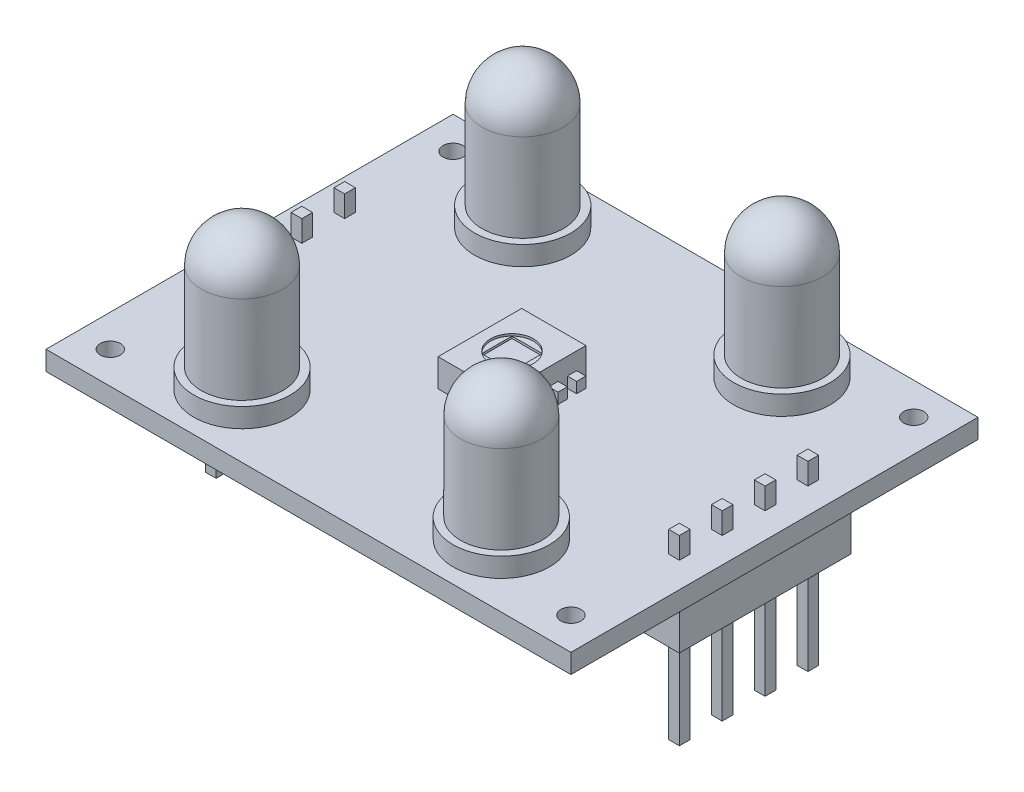
SolidWorks part; units mm, degrees
ref_plane "Plan de face" through (0, 0, 0) normal (0, 0, 1) x (1, 0, 0)
ref_plane "Plan de dessus" through (0, 0, 0) normal (0, 1, 0) x (1, 0, 0)
ref_plane "Plan de droite" through (0, 0, 0) normal (1, 0, 0) x (0, 0, -1)
sketch "Esquisse1" plane through (0, 0, 0) normal (0, 1, 0) x (1, 0, 0)
  line L1 (-15.5575, -12.065) -> (15.5575, -12.065)
  line L2 (-15.5575, -12.065) -> (-15.5575, 12.065)
  line L3 (-15.5575, 12.065) -> (15.5575, 12.065)
  line L4 (15.5575, -12.065) -> (15.5575, 12.065)
  line L5 (-15.5575, -12.065) -> (15.5575, 12.065) construction
  line L6 (-15.5575, 12.065) -> (15.5575, -12.065) construction
  line L7 (13.6525, -10.16) -> (-13.6525, -10.16) construction
  line L8 (13.6525, -10.16) -> (13.6525, 10.16) construction
  line L9 (13.6525, 10.16) -> (-13.6525, 10.16) construction
  line L10 (-13.6525, -10.16) -> (-13.6525, 10.16) construction
  line L11 (13.6525, -10.16) -> (-13.6525, 10.16) construction
  line L12 (13.6525, 10.16) -> (-13.6525, -10.16) construction
  circle A0 centre (-13.6525, 10.16) radius 0.5953
  circle A1 centre (13.6525, 10.16) radius 0.5953
  circle A2 centre (-13.6525, -10.16) radius 0.5953
  circle A3 centre (13.6525, -10.16) radius 0.5953
  point P0 (0, 0)
  point P6 (0, 0)
  dimension "D5" = 1.1906
  dimension "D1" = 31.115
  dimension "D2" = 24.13
  dimension "D3" = 1.905
  dimension "D4" = 1.905
extrude "Boss.-Extru.1" add sketch "Esquisse1" along normal mid plane 1.143
sketch "Esquisse2" plane through (0, 0, 0) normal (0, 0, 1) x (1, 0, 0)
  line L0 (-15.5575, 0.5715) -> (15.5575, 0.5715) construction
  line L1 (-1.905, 2.2225) -> (1.905, 2.2225)
  line L2 (-1.905, 2.2225) -> (-1.905, 0.5715)
  line L3 (-1.905, 0.5715) -> (1.905, 0.5715)
  line L4 (1.905, 2.2225) -> (1.905, 0.5715)
  line L5 (-1.905, 2.2225) -> (1.905, 0.5715) construction
  line L6 (-1.905, 0.5715) -> (1.905, 2.2225) construction
  point P0 (0, 1.397)
  dimension "D1" = 1.651
  dimension "D2" = 3.81
extrude "Boss.-Extru.2" add sketch "Esquisse2" along normal mid plane 4.953
sketch "Esquisse3" plane through (0, 0.5715, 0) normal (0, 1, 0) x (1, 0, 0)
  line L0 (1.905, -2.4765) -> (1.905, 2.4765) construction
  line L1 (1.905, 1.9262) -> (2.4553, 1.9262)
  line L2 (1.905, 1.9262) -> (1.905, 1.3758)
  line L3 (1.905, 1.3758) -> (2.4553, 1.3758)
  line L4 (2.4553, 1.9262) -> (2.4553, 1.3758)
  line L5 (2.1802, 1.3758) -> (2.1802, 0.8255) construction
  line L6 (1.905, 0.8255) -> (2.4553, 0.8255)
  line L7 (1.905, 0.8255) -> (1.905, 0.2752)
  line L8 (1.905, 0.2752) -> (2.4553, 0.2752)
  line L9 (2.4553, 0.8255) -> (2.4553, 0.2752)
  line L10 (1.905, -0.2752) -> (2.4553, -0.2752)
  line L11 (1.905, -0.2752) -> (1.905, -0.8255)
  line L12 (1.905, -0.8255) -> (2.4553, -0.8255)
  line L13 (2.4553, -0.2752) -> (2.4553, -0.8255)
  line L14 (1.905, -1.3758) -> (2.4553, -1.3758)
  line L15 (1.905, -1.3758) -> (1.905, -1.9262)
  line L16 (1.905, -1.9262) -> (2.4553, -1.9262)
  line L17 (2.4553, -1.3758) -> (2.4553, -1.9262)
  line L18 (2.1802, 0.2752) -> (2.1802, -0.2752) construction
  line L19 (2.1802, -0.8255) -> (2.1802, -1.3758) construction
  line L20 (2.1802, 1.9262) -> (2.1802, 2.4765) construction
  line L21 (2.1802, -1.9262) -> (2.1802, -2.4765) construction
  line L22 (-1.905, -2.4765) -> (1.905, -2.4765) construction
  line L23 (1.905, 2.4765) -> (-1.905, 2.4765) construction
extrude "Boss.-Extru.3" add sketch "Esquisse3" along normal blind 0.635
sketch "Esquisse9" plane through (0, -0.5715, 0) normal (0, -1, 0) x (1, 0, 0)
  line L0 (0, -5.2776) -> (0, 5.2776) construction
  line L1 (15, 5.08) -> (12.46, 5.08)
  line L2 (15, 5.08) -> (15, -5.08)
  line L3 (15, -5.08) -> (12.46, -5.08)
  line L4 (12.46, 5.08) -> (12.46, -5.08)
  line L5 (0, -1.5367) -> (0, 1.5367) construction
  point P6 (12.46, 0)
  dimension "D1" = 2.54
  dimension "D2" = 10.16
  dimension "D3" = 30
extrude "Boss.-Extru.6" add sketch "Esquisse9" along normal blind 2.667
sketch "Esquisse10" plane through (0, -3.2385, 0) normal (0, -1, 0) x (1, 0, 0)
  line L0 (12.46, 0) -> (15, 5.08) construction
  line L1 (12.46, 5.08) -> (12.46, -5.08) construction
  line L2 (13.73, 2.54) -> (13.73, 5.08) construction
  line L3 (15, 5.08) -> (12.46, 5.08) construction
  line L4 (12.46, 0) -> (15, -5.08) construction
  line L5 (13.73, -2.54) -> (13.73, -5.08) construction
  line L6 (12.46, -5.08) -> (15, -5.08) construction
  line L7 (13.73, 2.54) -> (13.73, 0) construction
  line L8 (13.4125, 4.1275) -> (14.0475, 4.1275)
  line L9 (13.4125, 4.1275) -> (13.4125, 3.4925)
  line L10 (13.4125, 3.4925) -> (14.0475, 3.4925)
  line L11 (14.0475, 4.1275) -> (14.0475, 3.4925)
  line L12 (13.4125, 4.1275) -> (14.0475, 3.4925) construction
  line L13 (13.4125, 3.4925) -> (14.0475, 4.1275) construction
  line L14 (3.0035, 0) -> (-3.0035, 0) construction
  line L15 (13.73, 0) -> (13.73, -2.54) construction
  line L17 (13.4125, 1.5875) -> (14.0475, 1.5875)
  line L18 (13.4125, 1.5875) -> (13.4125, 0.9525)
  line L19 (13.4125, 0.9525) -> (14.0475, 0.9525)
  line L20 (14.0475, 1.5875) -> (14.0475, 0.9525)
  line L21 (13.4125, 1.5875) -> (14.0475, 0.9525) construction
  line L22 (13.4125, 0.9525) -> (14.0475, 1.5875) construction
  line L23 (13.4125, -0.9525) -> (14.0475, -0.9525)
  line L24 (13.4125, -0.9525) -> (13.4125, -1.5875)
  line L25 (13.4125, -1.5875) -> (14.0475, -1.5875)
  line L26 (14.0475, -0.9525) -> (14.0475, -1.5875)
  line L27 (13.4125, -0.9525) -> (14.0475, -1.5875) construction
  line L28 (13.4125, -1.5875) -> (14.0475, -0.9525) construction
  line L29 (13.4125, -3.4925) -> (14.0475, -3.4925)
  line L30 (13.4125, -3.4925) -> (13.4125, -4.1275)
  line L31 (13.4125, -4.1275) -> (14.0475, -4.1275)
  line L32 (14.0475, -3.4925) -> (14.0475, -4.1275)
  line L33 (13.4125, -3.4925) -> (14.0475, -4.1275) construction
  line L34 (13.4125, -4.1275) -> (14.0475, -3.4925) construction
  point P13 (13.73, 3.81)
  point P18 (13.73, 1.27)
  point P28 (13.73, -1.27)
  point P33 (13.73, -3.81)
  dimension "D1" = 0.635
extrude "Boss.-Extru.7" add sketch "Esquisse10" along normal blind 5.715 and the other way offset from surface (5.08 mm away) 1.27 other way up to face at (0, 0.5715, 0)
mirror "Symétrie1" about plane through (0, 0, 0) normal (1, 0, 0) of "Boss.-Extru.7", "Boss.-Extru.3"
mirror "Symétrie2" about plane through (0, 0, 0) normal (1, 0, 0) of "Boss.-Extru.6"
sketch "Esquisse4" plane through (0, 2.2225, 0) normal (0, 1, 0) x (1, 0, 0)
  circle A0 centre (0, 0) radius 1.27
  dimension "D1" = 2.54
extrude "Enlèv. mat.-Extru.1" cut sketch "Esquisse4" against normal blind 0.127
sketch "Esquisse5" plane through (0, 2.0955, 0) normal (0, 1, 0) x (1, 0, 0)
  line L1 (0.898, -0.898) -> (-0.898, -0.898)
  line L2 (0.898, -0.898) -> (0.898, 0.898)
  line L3 (0.898, 0.898) -> (-0.898, 0.898)
  line L4 (-0.898, -0.898) -> (-0.898, 0.898)
  line L5 (0.898, -0.898) -> (-0.898, 0.898) construction
  line L6 (0.898, 0.898) -> (-0.898, -0.898) construction
  circle A0 centre (0, 0) radius 1.27 construction
  point P0 (0, 0)
extrude "Enlèv. mat.-Extru.2" cut sketch "Esquisse5" against normal blind 0.127
sketch "Esquisse6" plane through (0, 0.5715, 0) normal (0, 1, 0) x (1, 0, 0)
  line L1 (7.6835, -8.3185) -> (-7.6835, -8.3185) construction
  line L2 (7.6835, -8.3185) -> (7.6835, 8.3185) construction
  line L3 (7.6835, 8.3185) -> (-7.6835, 8.3185) construction
  line L4 (-7.6835, -8.3185) -> (-7.6835, 8.3185) construction
  line L5 (7.6835, -8.3185) -> (-7.6835, 8.3185) construction
  line L6 (7.6835, 8.3185) -> (-7.6835, -8.3185) construction
  point P7 (-7.6835, 8.3185)
  point P8 (7.6835, 8.3185)
  point P9 (7.6835, -8.3185)
  point P10 (-7.6835, -8.3185)
  point P12 (0, 0)
  dimension "D1" = 15.367
  dimension "D2" = 16.637
sketch "Esquisse7" plane through (0, 0.5715, 0) normal (0, 1, 0) x (1, 0, 0)
  circle A0 centre (-7.6835, 8.3185) radius 2.8575
  dimension "D1" = 5.715
extrude "Boss.-Extru.4" add sketch "Esquisse7" along normal blind 1.143
sketch "Esquisse8" plane through (0, 1.7145, 0) normal (0, 1, 0) x (1, 0, 0)
  circle A0 centre (-7.6835, 8.3185) radius 2.413
  dimension "D1" = 4.826
extrude "Boss.-Extru.5" add sketch "Esquisse8" along normal blind 7.62
fillet "Congé1" radius 2.413 1 edges at (-7.6835, 9.3345, -5.9055)
pattern_sketch "Répét. par esquisse1" of "Boss.-Extru.4", "Boss.-Extru.5", "Congé1" driven by "Esquisse6"
